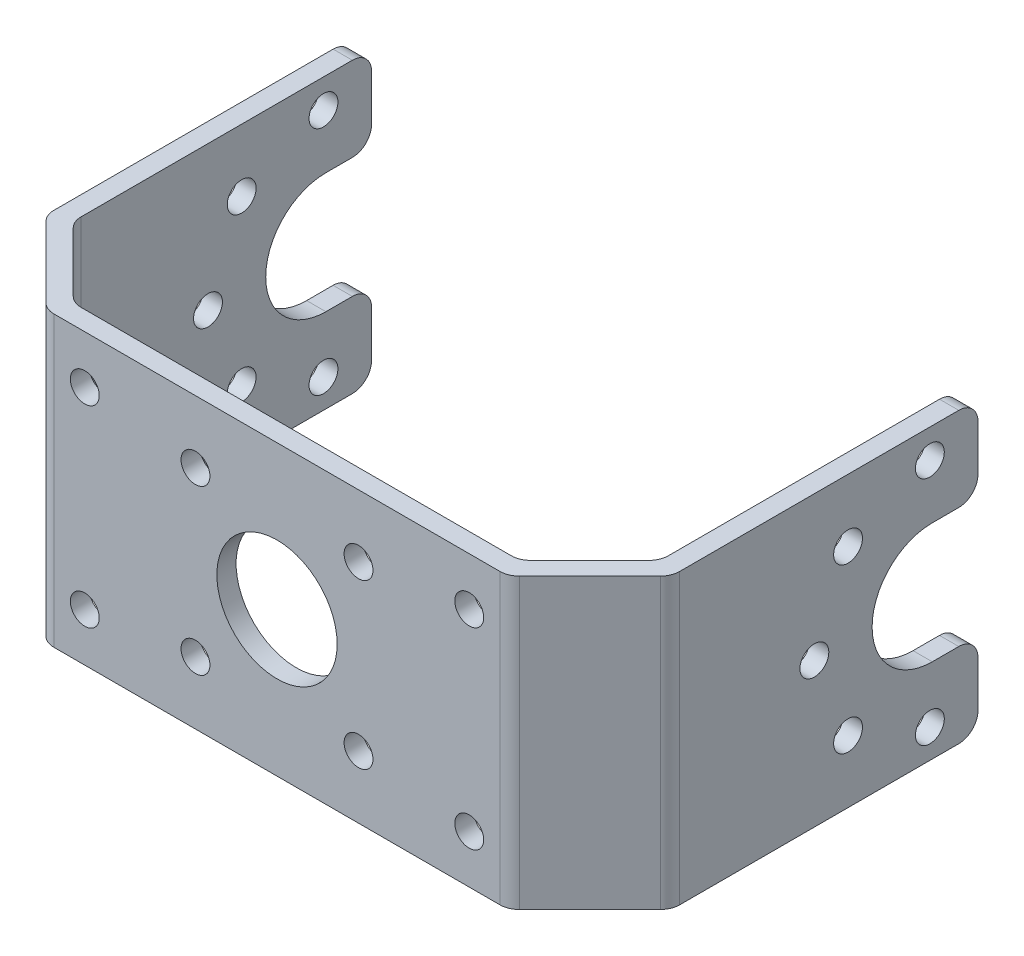
SolidWorks part; units mm, degrees
ref_plane "Front Plane" through (0, 0, 0) normal (0, 0, 1) x (1, 0, 0)
ref_plane "Top Plane" through (0, 0, 0) normal (0, 1, 0) x (1, 0, 0)
ref_plane "Right Plane" through (0, 0, 0) normal (1, 0, 0) x (0, 0, -1)
sketch "Sketch1" plane through (0, 0, 0) normal (0, 1, 0) x (1, 0, 0)
  line L6 (0, -38.3284) -> (23.1716, -38.3284)
  line L7 (0, -38.3284) -> (0, -40.3284)
  line L8 (0, -40.3284) -> (24, -40.3284)
  line L9 (30.5, 0) -> (30.5, -31)
  line L10 (30.5, -31) -> (23.1716, -38.3284)
  line L11 (32.5, 0) -> (32.5, -31.8284)
  line L13 (30.5, 0) -> (32.5, 0)
  line L19 (26.8358, -34.6642) -> (28.25, -36.0784) construction
  line L20 (24, -40.3284) -> (32.5, -31.8284)
  point P10 (0, -38.3284)
  point P31 (28.25, -36.0784)
  dimension "D1" = 30.5
  dimension "D2" = 24
  dimension "D3" = 2
  dimension "D4" = 2
  dimension "D5" = 31
  dimension "D6" = 2
extrude "Boss-Extrude2" add sketch "Sketch1" along normal blind 30
mirror "Mirror1" about plane through (0, 0, 0) normal (1, 0, 0) of "Boss-Extrude2"
sketch "Sketch2" plane through (32.5, 0, 0) normal (1, 0, 0) x (0, 0, -1)
  line L0 (0, 15) -> (-11, 15) construction
  line L1 (0, 30) -> (0, 0) construction
  line L2 (-11, 15) -> (-13.5, 15) construction
  line L3 (-4.75, 21.25) -> (0, 21.25)
  line L4 (-4.75, 8.75) -> (0, 8.75)
  line L5 (0, 21.25) -> (0, 8.75)
  line L6 (-5, 27) -> (-5, 3) construction
  line L7 (-13.5, 15) -> (-17, 15) construction
  line L19 (-13.5, 23.5) -> (-13.5, 6.5) construction
  arc A0 (-4.75, 21.25) -> (-4.75, 8.75) centre (-4.75, 15) ccw
  circle A2 centre (-17, 15) radius 1.5
  circle A3 centre (-5, 3) radius 1.5
  circle A4 centre (-13.5, 6.5) radius 1.5
  circle A5 centre (-13.5, 23.5) radius 1.5
  circle A6 centre (-5, 27) radius 1.5
  point P7 (-11, 15)
  point P23 (-5, 15)
extrude "Cut-Extrude1" cut sketch "Sketch2" against normal through all
sketch "Sketch3" plane through (0, 0, 40.3284) normal (0, 0, 1) x (1, 0, 0)
  line L0 (0, 0) -> (0, 30) construction
  line L1 (-8.4705, 6.5) -> (-19.9705, 6.5) construction
  line L2 (-24, 0) -> (24, 0) construction
  line L3 (-8.4705, 23.5) -> (-8.4705, 6.5) construction
  line L4 (-24, 30) -> (24, 30) construction
  line L5 (0, 15) -> (8.4705, 15) construction
  line L6 (0, 15) -> (-8.5, 15) construction
  line L7 (8.4705, 23.5) -> (8.4705, 6.5) construction
  line L8 (-8.4705, 23.5) -> (-19.9705, 23.5) construction
  line L9 (-8.4705, 23.5) -> (8.4705, 6.5) construction
  line L11 (8.4705, 23.5) -> (19.9705, 23.5) construction
  line L12 (8.4705, 6.5) -> (19.9705, 6.5) construction
  circle A0 centre (0, 15) radius 6.25
  circle A1 centre (8.4705, 6.5) radius 1.5
  circle A2 centre (8.4705, 23.5) radius 1.5
  circle A7 centre (19.9705, 5) radius 1.5
  circle A8 centre (19.9705, 25) radius 1.5
  circle A9 centre (-19.9705, 5) radius 1.5
  circle A10 centre (-8.4705, 6.5) radius 1.5
  circle A11 centre (-19.9705, 25) radius 1.5
  circle A12 centre (-8.4705, 23.5) radius 1.5
  point P13 (8.4705, 15)
  point P16 (-8.5, 15)
  point P34 (0, 15)
  dimension "D1" = 11.5
  dimension "D2" = 3
  dimension "D3" = 3
  dimension "D4" = 3
  dimension "D5" = 3
  dimension "D7" = 12.5
  dimension "D6" = 17
extrude "Cut-Extrude2" cut sketch "Sketch3" against normal blind 10
fillet "Fillet1" radius 2 16 edges at (-30.5, 15, 31) (-23.1716, 15, 38.3284) (-24, 15, 40.3284) (-32.5, 15, 31.8284) (-31.5, 8.75, 0) (-31.5, 0, 0) (-31.5, 21.25, 0) (-31.5, 30, 0) (31.5, 0, 0) (31.5, 8.75, 0) (31.5, 21.25, 0) (31.5, 30, 0) (30.5, 15, 31) (23.1716, 15, 38.3284) (32.5, 15, 31.8284) (24, 15, 40.3284)
